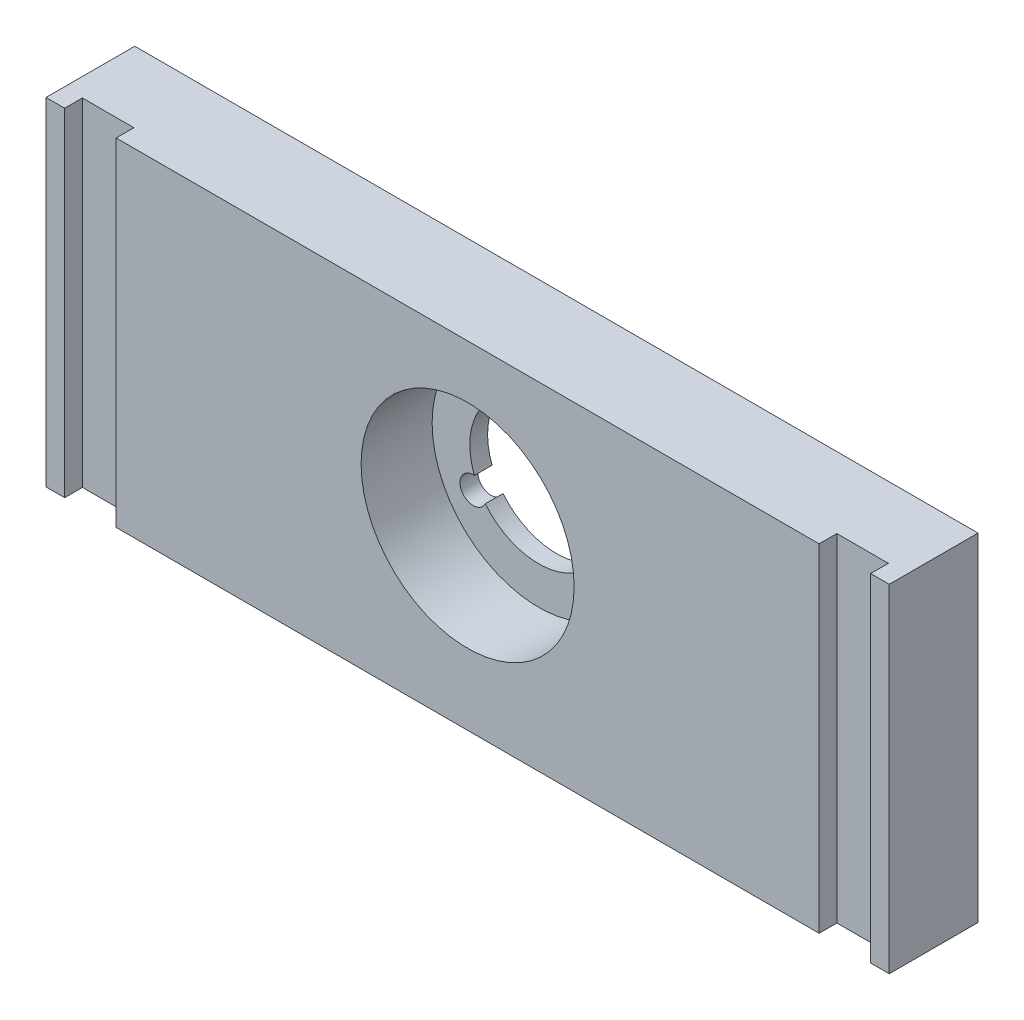
SolidWorks part; units mm, degrees
ref_plane "Plan de face" through (0, 0, 0) normal (0, 0, 1) x (1, 0, 0)
ref_plane "Plan de dessus" through (0, 0, 0) normal (0, 1, 0) x (1, 0, 0)
ref_plane "Plan de droite" through (0, 0, 0) normal (1, 0, 0) x (0, 0, -1)
sketch "Esquisse1" plane through (0, 0, 0) normal (0, 0, 1) x (1, 0, 0)
  line L0 (3, -2) -> (98, -2)
  line L1 (98, -2) -> (98, -40)
  line L2 (98, -40) -> (3, -40)
  line L3 (3, -40) -> (3, -2)
  line L4 (0, 0) -> (101, -40) construction
  line L5 (50.5, -20) -> (50.5, -10.1968) construction
  line L6 (50.5, -20) -> (33.461, -20) construction
  arc A0 (49.2636, -12.3493) -> (43.2561, -22.7546) centre (50.5, -20) ccw
  arc A1 (51.7364, -12.3493) -> (49.2636, -12.3493) centre (50.5, -11.5) ccw
  arc A2 (56.5075, -24.8961) -> (57.7439, -22.7546) centre (57.8612, -24.25) ccw
  arc A3 (43.2561, -22.7546) -> (44.4925, -24.8961) centre (43.1388, -24.25) ccw
  arc A4 (57.7439, -22.7546) -> (51.7364, -12.3493) centre (50.5, -20) ccw
  arc A5 (44.4925, -24.8961) -> (56.5075, -24.8961) centre (50.5, -20) ccw
extrude "Extrusion1" add sketch "Esquisse1" along normal blind 10
sketch "Esquisse3" plane through (0, 0, 10) normal (0, 0, 1) x (1, 0, 0)
  circle A0 centre (50.5, -20) radius 12
extrude "Extrusion3" cut sketch "Esquisse3" against normal blind 8
sketch "Esquisse4" plane through (0, 0, 10) normal (0, 0, 1) x (1, 0, 0)
  line L0 (5.1, -2) -> (10.9, -2)
  line L2 (5.1, -40) -> (5.1, -2)
  line L3 (98, -2) -> (3, -2) construction
  line L4 (10.9, -40) -> (10.9, -2)
  line L5 (10.9, -40) -> (5.1, -40)
  line L6 (3, -40) -> (98, -40) construction
  line L7 (50.5, -20) -> (50.5, 3.4527) construction
  line L8 (90.1, -40) -> (95.9, -40)
  line L9 (90.1, -40) -> (90.1, -2)
  line L10 (95.9, -40) -> (95.9, -2)
  line L11 (95.9, -2) -> (90.1, -2)
extrude "Extrusion4" cut sketch "Esquisse4" against normal blind 2
